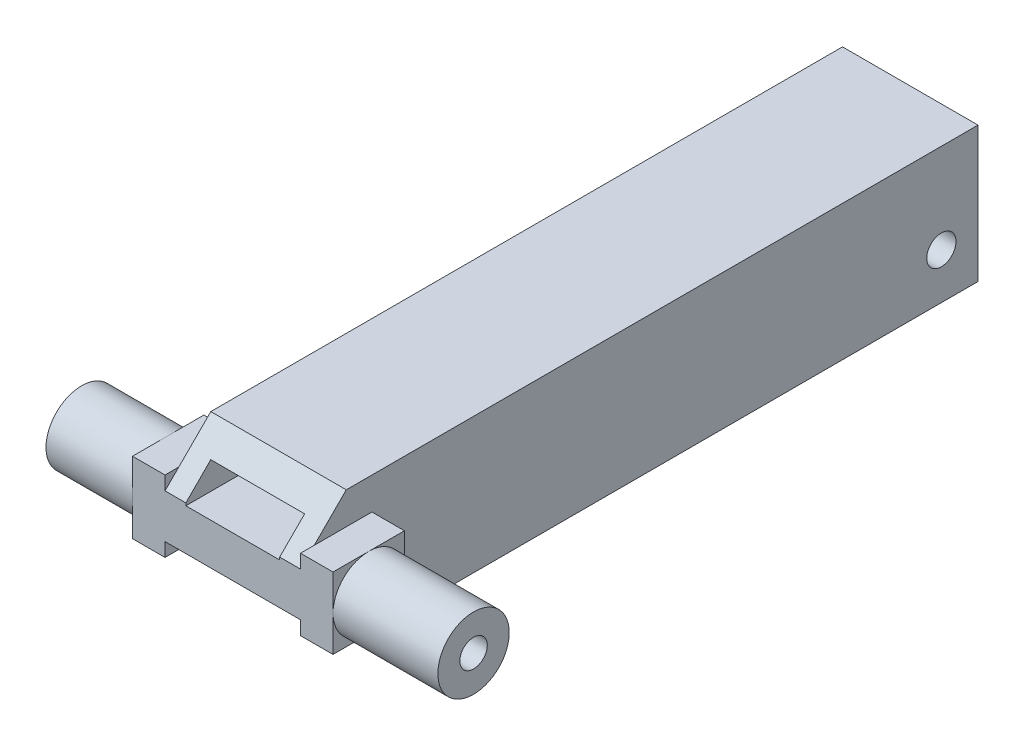
SolidWorks part; units mm, degrees
ref_plane "Спереди" through (0, 0, 0) normal (0, 0, 1) x (1, 0, 0)
ref_plane "Сверху" through (0, 0, 0) normal (0, 1, 0) x (1, 0, 0)
ref_plane "Справа" through (0, 0, 0) normal (1, 0, 0) x (0, 0, -1)
sketch "Эскиз1" plane through (0, 0, 0) normal (1, 0, 0) x (0, 0, -1)
  line L1 (37, -7.4) -> (-37, -7.4)
  line L2 (37, -7.4) -> (37, 7.4)
  line L3 (37, 7.4) -> (-37, 7.4)
  line L4 (-37, -7.4) -> (-37, 7.4)
  line L5 (37, -7.4) -> (-37, 7.4) construction
  line L6 (37, 7.4) -> (-37, -7.4) construction
  point P0 (0, 0)
  dimension "D1" = 14.8
  dimension "D2" = 74
extrude "Бобышка-Вытянуть1" add sketch "Эскиз1" along normal blind 14.8
sketch "Эскиз2" plane through (0, 0, -37) normal (0, 0, -1) x (-1, 0, 0)
  line L0 (0, 7.4) -> (-14.8, -7.4) construction
  line L2 (-2.275, -5.125) -> (-12.525, -5.125)
  line L3 (-2.275, -5.125) -> (-2.275, 5.125)
  line L4 (-2.275, 5.125) -> (-12.525, 5.125)
  line L5 (-12.525, -5.125) -> (-12.525, 5.125)
  line L6 (-2.275, -5.125) -> (-12.525, 5.125) construction
  line L7 (-2.275, 5.125) -> (-12.525, -5.125) construction
  point P4 (-7.4, 0)
  dimension "D1" = 10.25
extrude "Вырез-Вытянуть1" cut sketch "Эскиз2" against normal blind 65
sketch "Эскиз3" plane through (14.8, 0, 0) normal (1, 0, 0) x (0, 0, -1)
  line L0 (37, 0) -> (-37, 0) construction
  line L1 (37, -7.4) -> (37, 7.4) construction
  line L2 (-37, 7.4) -> (-37, -7.4) construction
  circle A0 centre (-33.1, 0) radius 3.9
  dimension "D1" = 7.8
extrude "Бобышка-Вытянуть2" add sketch "Эскиз3" along normal blind 15
sketch "Эскиз4" plane through (0, 0, 0) normal (-1, 0, 0) x (0, 0, 1)
  line L0 (37, 0) -> (-37, 0) construction
  line L1 (37, 7.4) -> (37, -7.4) construction
  line L2 (-37, -7.4) -> (-37, 7.4) construction
  circle A0 centre (33.1, 0) radius 3.9
  dimension "D1" = 7.8
extrude "Бобышка-Вытянуть3" add sketch "Эскиз4" along normal blind 13
chamfer "Фаска1" distance 5 angle 45 2 edges at (7.4, -7.4, 37) (7.4, 7.4, 37)
sketch "Эскиз8" plane through (29.8, 0, 0) normal (1, 0, 0) x (0, 0, -1)
  circle A0 centre (-33.1, 0) radius 1.45
  dimension "D1" = 2.9
extrude "Вырез-Вытянуть4" cut sketch "Эскиз8" against normal through all
sketch "Эскиз9" plane through (0, 0, 0) normal (-1, 0, 0) x (0, 0, 1)
  line L1 (37, -3.9) -> (29.2, -3.9)
  line L2 (37, -3.9) -> (37, 3.9)
  line L3 (37, 3.9) -> (29.2, 3.9)
  line L4 (29.2, -3.9) -> (29.2, 3.9)
  line L5 (37, -3.9) -> (29.2, 3.9) construction
  line L6 (37, 3.9) -> (29.2, -3.9) construction
  circle A0 centre (33.1, 0) radius 3.9 construction
  circle A1 centre (33.1, 0) radius 1.5
  point P0 (33.1, 0)
  point P6 (29.2, 0)
  point P11 (33.1, 3.9)
  dimension "D1" = 3
extrude "Бобышка-Вытянуть4" add sketch "Эскиз9" along normal blind 3.55
sketch "Эскиз10" plane through (14.8, 0, 0) normal (1, 0, 0) x (0, 0, -1)
  line L1 (-37, -3.9) -> (-29.2, -3.9)
  line L2 (-37, -3.9) -> (-37, 3.9)
  line L3 (-37, 3.9) -> (-29.2, 3.9)
  line L4 (-29.2, -3.9) -> (-29.2, 3.9)
  line L5 (-37, -3.9) -> (-29.2, 3.9) construction
  line L6 (-37, 3.9) -> (-29.2, -3.9) construction
  circle A0 centre (-33.1, 0) radius 3.9 construction
  point P0 (-33.1, 0)
  point P6 (-29.2, 0)
  point P9 (-33.1, 3.9)
extrude "Бобышка-Вытянуть5" add sketch "Эскиз10" along normal blind 3.55
sketch "Sketch1" plane through (0, 0, 0) normal (-1, 0, 0) x (0, 0, 1)
  line L0 (-33, 7.4) -> (-33, -7.4) construction
  line L7 (-37, 7.4) -> (32, 7.4) construction
  line L8 (32, -7.4) -> (-37, -7.4) construction
  line L9 (-37, -7.4) -> (-37, 7.4) construction
  circle A0 centre (-33, -2.4) radius 1.6
  dimension "D1" = 3.2
  dimension "D2" = 4
  dimension "D3" = 5
extrude "Cut-Extrude1" cut sketch "Sketch1" against normal through all
sketch "Sketch2" plane through (29.8, 0, 0) normal (1, 0, 0) x (0, 0, -1)
  circle A0 centre (-33.1, 0) radius 1.5
extrude "Cut-Extrude2" cut sketch "Sketch2" against normal through all
sketch "Sketch3" plane through (0, 0, 28) normal (0, 0, -1) x (-1, 0, 0)
  line L0 (-7.4, 5.125) -> (-7.4, -5.125) construction
  line L1 (-2.275, 5.125) -> (-12.525, 5.125) construction
  line L2 (-12.525, -5.125) -> (-2.275, -5.125) construction
  line L4 (-2.275, 2.125) -> (-12.525, 2.125)
  line L5 (-2.275, 2.125) -> (-2.275, 5.125)
  line L6 (-2.275, 5.125) -> (-12.525, 5.125)
  line L7 (-12.525, 2.125) -> (-12.525, 5.125)
  line L8 (-2.275, 2.125) -> (-12.525, 5.125) construction
  line L9 (-2.275, 5.125) -> (-12.525, 2.125) construction
  point P6 (-7.4, 3.625)
  dimension "D1" = 3
extrude "Cut-Extrude3" cut sketch "Sketch3" against normal through all
